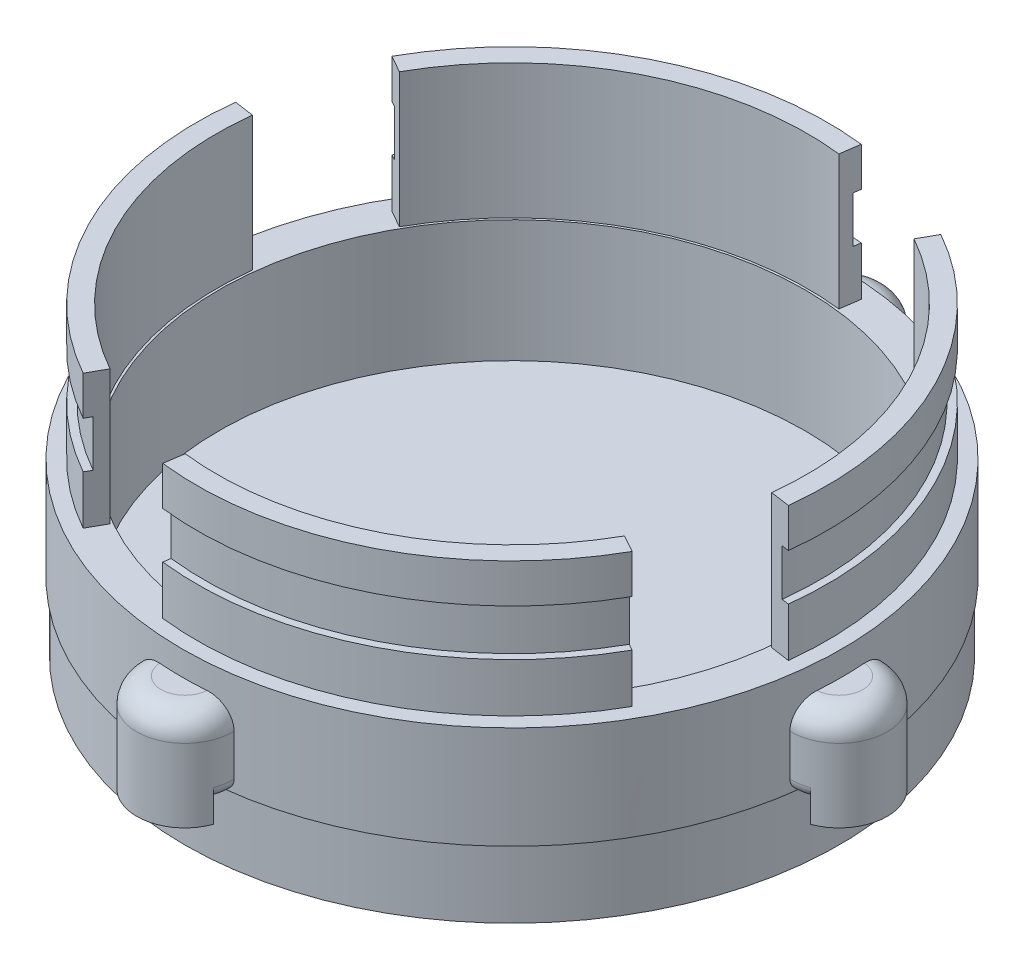
SolidWorks part; units mm, degrees
ref_plane "Front Plane" through (0, 0, 0) normal (0, 0, 1) x (1, 0, 0)
ref_plane "Top Plane" through (0, 0, 0) normal (0, 1, 0) x (1, 0, 0)
ref_plane "Right Plane" through (0, 0, 0) normal (1, 0, 0) x (0, 0, -1)
sketch "Sketch1" plane through (0, 0, 0) normal (0, 1, 0) x (1, 0, 0)
  circle A0 centre (0, 0) radius 30.1625
  circle A1 centre (0, 0) radius 26.9875
sketch "Sketch3" plane through (0, 0, 0) normal (0, 1, 0) x (1, 0, 0)
  line L0 (30.48, 0) -> (34.29, 0) construction
  circle A0 centre (0, 0) radius 34.29
  circle A1 centre (0, 0) radius 30.48
  dimension "D1" = 60.96
  dimension "D2" = 3.81
extrude "Boss-Extrude2" add sketch "Sketch3" along normal blind 12.7 separate body
sketch "Sketch5" plane through (0, 0, 0) normal (0, 1, 0) x (1, 0, 0)
  line L0 (28.559, -16.0622) -> (26.7702, -15.0561)
  line L1 (0, 0) -> (32.5458, -3.792) construction
  line L2 (-3.4981, -30.5138) -> (-3.792, -32.5458)
  line L3 (-16.0622, -28.559) -> (-15.0561, -26.7702)
  line L4 (-30.5138, 3.4981) -> (-32.5458, 3.792)
  line L5 (-28.559, 16.0622) -> (-26.7702, 15.0561)
  line L6 (3.4981, 30.5138) -> (3.792, 32.5458)
  line L7 (0, 0) -> (3.792, 32.5458) construction
  line L8 (0, 0) -> (-28.559, 16.0622) construction
  line L9 (0, 0) -> (-32.5458, 3.792) construction
  line L10 (-32.5458, 3.792) -> (-32.5902, 3.8035)
  line L11 (0, 0) -> (-16.0622, -28.559) construction
  line L12 (0, 0) -> (-3.792, -32.5458) construction
  line L13 (28.559, -16.0622) -> (0, 0) construction
  line L14 (30.5138, -3.4981) -> (32.5458, -3.792)
  line L15 (0, 0) -> (16.0622, 28.559) construction
  line L16 (16.0622, 28.559) -> (15.0561, 26.7702)
  arc A0 (-3.4981, -30.5138) -> (26.7702, -15.0561) centre (0, 0) ccw
  arc A1 (28.559, -16.0622) -> (-3.792, -32.5458) centre (0, 0) cw
  arc A2 (-30.5138, 3.4981) -> (-15.0561, -26.7702) centre (0, 0) ccw
  arc A3 (-16.0622, -28.559) -> (-32.5458, 3.792) centre (0, 0) cw
  arc A4 (3.4981, 30.5138) -> (-26.7702, 15.0561) centre (0, 0) ccw
  arc A5 (-28.559, 16.0622) -> (3.792, 32.5458) centre (0, 0) cw
  arc A12 (30.5138, -3.4981) -> (15.0561, 26.7702) centre (0, 0) ccw
  arc A13 (16.0622, 28.559) -> (32.5458, -3.792) centre (0, 0) cw
  point P16 (0, 0)
  point P31 (0, 0)
  dimension "D1" = 2.032
  dimension "D2" = 4
extrude "Boss-Extrude6" add sketch "Sketch5" along normal blind 26.67 separate body contours A1 L0 A0 L2 | A5 L5 A4 L6 | A3 L3 A2 L4 | A12 L16 A13 L14
sketch "Sketch7" plane through (0, 0, 0) normal (0, 1, 0) x (1, 0, 0)
  line L0 (32.004, 0) -> (34.036, 0) construction
  circle A0 centre (0, 0) radius 34.036
  circle A1 centre (0, 0) radius 32.004
  dimension "D1" = 68.072
  dimension "D2" = 2.032
extrude "Cut-Extrude2" cut sketch "Sketch7" along normal blind 4.826 from offset 17.78
sketch "Sketch8" plane through (0, 0, 0) normal (0, 1, 0) x (1, 0, 0)
  circle A0 centre (0, 0) radius 34.036
  circle A1 centre (0, 0) radius 5
  dimension "D1" = 68.072
  dimension "D2" = 10
extrude "Boss-Extrude7" add sketch "Sketch8" against normal blind 5.08
sketch "Sketch10" plane through (0, 0, 0) normal (0, 1, 0) x (1, 0, 0)
  line L0 (32.004, 0) -> (34.036, 0) construction
  circle A0 centre (0, 0) radius 34.036
  circle A1 centre (0, 0) radius 32.004
  arc A2 (0, -39.0412) -> (4.9916, -33.668) centre (0, -34.036) ccw
  arc A3 (0, -39.0412) -> (-4.9916, -33.668) centre (0, -34.036) cw
  arc A4 (-39.0412, 0) -> (-33.668, 4.9916) centre (-34.036, 0) cw
  arc A5 (-39.0412, 0) -> (-33.668, -4.9916) centre (-34.036, 0) ccw
  arc A6 (0, 39.0412) -> (4.9916, 33.668) centre (0, 34.036) cw
  arc A7 (0, 39.0412) -> (-4.9916, 33.668) centre (0, 34.036) ccw
  arc A8 (39.0412, 0) -> (33.668, -4.9916) centre (34.036, 0) cw
  arc A9 (39.0412, 0) -> (33.668, 4.9916) centre (34.036, 0) ccw
  point P24 (0, 0)
  dimension "D1" = 68.072
  dimension "D2" = 2.032
extrude "Boss-Extrude8" add sketch "Sketch10" along normal blind 10.16 contours A4 A5 A0 | A3 A2 A0 | A8 A9 A0 | A6 A7 A0
fillet "Fillet1" radius 2.54 4 edges at (39.0412, 10.16, 0) (0, 10.16, -39.0412) (-39.0412, 10.16, 0) (0, 10.16, 39.0412)
sketch "Sketch11" plane through (0, 0, 0) normal (0, 1, 0) x (1, 0, 0)
  line L0 (36.068, 0) -> (34.036, 0) construction
  circle A0 centre (0, 0) radius 34.036
  circle A1 centre (0, 0) radius 36.068
  point P24 (0, 0)
  dimension "D1" = 68.072
  dimension "D2" = 2.032
extrude "Cut-Extrude3" cut sketch "Sketch11" along normal blind 2.032
fillet "Fillet2" radius 1.27 8 edges at (-4.9375, 2.032, -34.8561) (4.9375, 2.032, -34.8561) (-34.8561, 2.032, 4.9375) (-34.8561, 2.032, -4.9375) (4.9375, 2.032, 34.8561) (-4.9375, 2.032, 34.8561) (34.8561, 2.032, -4.9375) (34.8561, 2.032, 4.9375)
